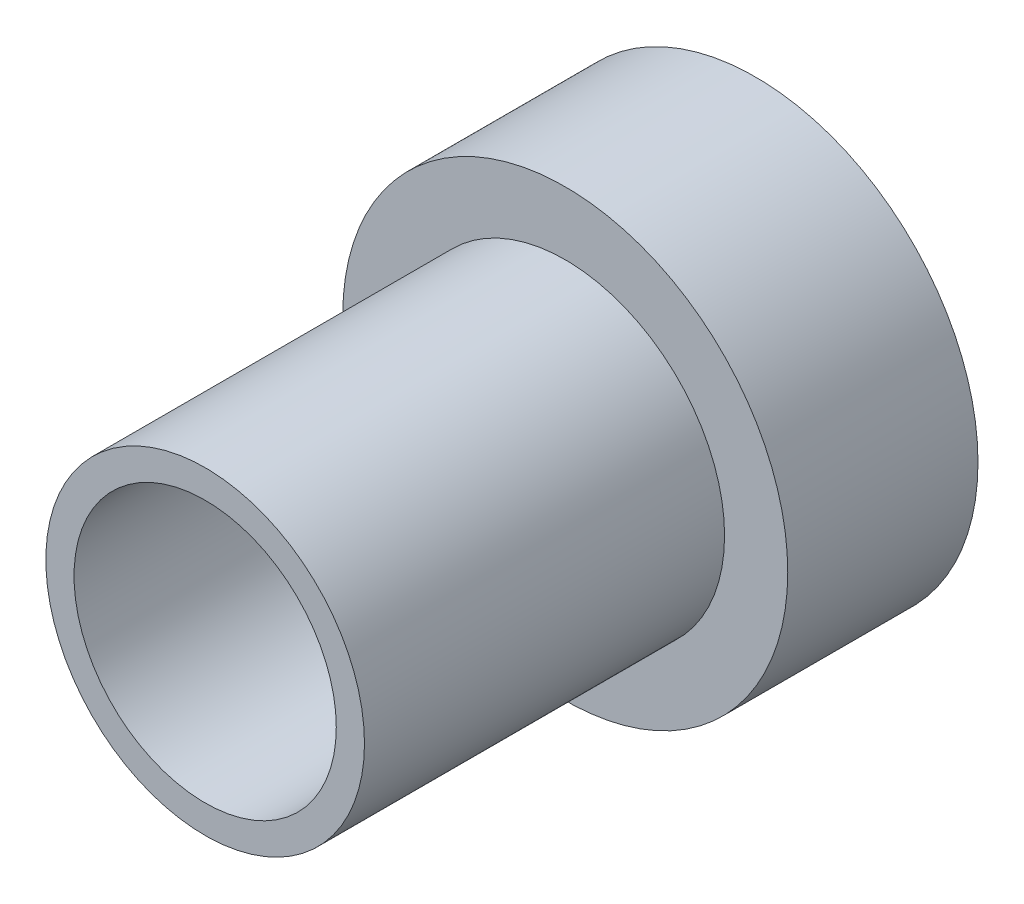
SolidWorks part; units mm, degrees
material "3003 Alloy"
ref_plane "Front Plane" through (0, 0, 0) normal (0, 0, 1) x (1, 0, 0)
ref_plane "Top Plane" through (0, 0, 0) normal (0, 1, 0) x (1, 0, 0)
ref_plane "Right Plane" through (0, 0, 0) normal (1, 0, 0) x (0, 0, -1)
sketch "Sketch1" plane through (0, 0, 0) normal (0, 0, 1) x (1, 0, 0)
  circle A0 centre (0, 0) radius 4.1593
  circle A1 centre (0, 0) radius 2.4511
  dimension "D1" = 4.9022
  dimension "D2" = 8.3185
extrude "Boss-Extrude1" add sketch "Sketch1" along normal blind 10.287
sketch "Sketch2" plane through (0, 0, 10.287) normal (0, 0, 1) x (1, 0, 0)
  circle A0 centre (0, 0) radius 2.9781
  dimension "D1" = 5.9563
extrude "Cut-Extrude1" cut sketch "Sketch2" against normal blind 6.731 flip side to cut
chamfer "Chamfer1" distance 1.778 angle 37 1 edges at (2.4511, 0, 0)
